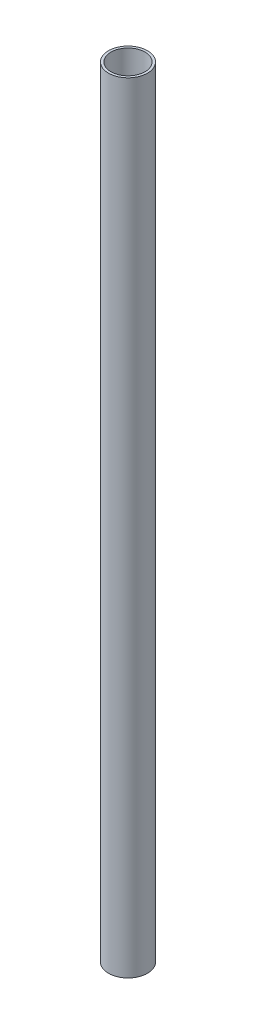
SolidWorks part; units mm, degrees
material "ASTM A36 Steel"
ref_plane "Front Plane" through (0, 0, 0) normal (0, 0, 1) x (1, 0, 0)
ref_plane "Top Plane" through (0, 0, 0) normal (0, 1, 0) x (1, 0, 0)
ref_plane "Right Plane" through (0, 0, 0) normal (1, 0, 0) x (0, 0, -1)
sketch "Sketch1" plane through (0, 0, 0) normal (0, 1, 0) x (1, 0, 0)
  circle A0 centre (0, 0) radius 44.45
  circle A1 centre (0, 0) radius 50.8
  dimension "D1" = 101.6
  dimension "D2" = 88.9
extrude "Boss-Extrude1" add sketch "Sketch1" along normal blind 2032
